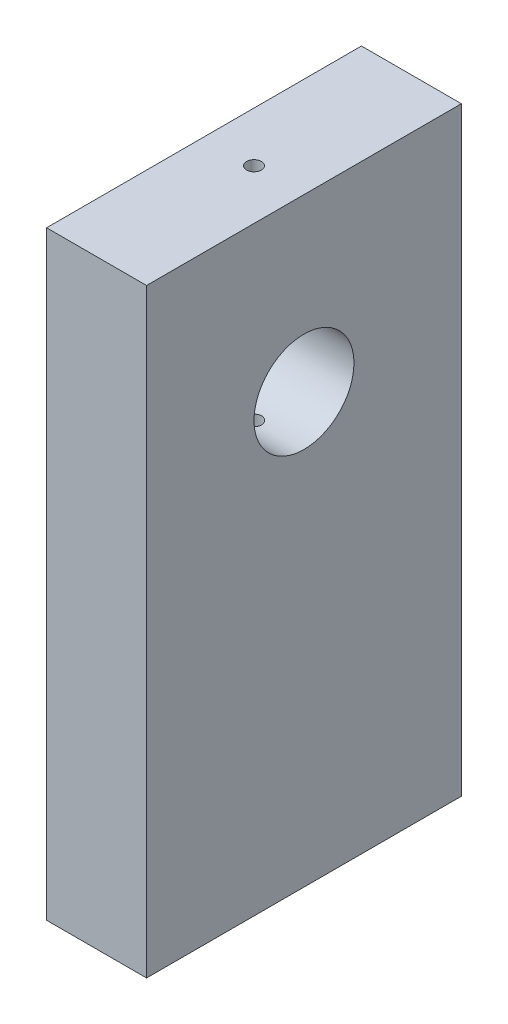
SolidWorks part; units mm, degrees
material "1060 Alloy"
ref_plane "Front Plane" through (0, 0, 0) normal (0, 0, 1) x (1, 0, 0)
ref_plane "Top Plane" through (0, 0, 0) normal (0, 1, 0) x (1, 0, 0)
ref_plane "Right Plane" through (0, 0, 0) normal (1, 0, 0) x (0, 0, -1)
sketch "Sketch11" plane through (0, 0, 0) normal (0, 1, 0) x (1, 0, 0)
  line L1 (0, -28.0311) -> (12.7, -28.0311)
  line L2 (0, -28.0311) -> (0, 11.9689)
  line L3 (0, 11.9689) -> (12.7, 11.9689)
  line L4 (12.7, -28.0311) -> (12.7, 11.9689)
  dimension "D1" = 12.7
extrude "Boss-Extrude2" add sketch "Sketch11" along normal blind 76.2
sketch "Sketch12" plane through (12.7, 0, 0) normal (1, 0, 0) x (0, 0, -1)
  line L1 (-8.0311, 76.2) -> (-8.0311, 1.8836) construction
  line L3 (-28.0311, 0) -> (11.9689, 0) construction
  line L5 (-28.0311, 76.2) -> (-28.0311, 0) construction
  circle A0 centre (-8.0311, 54.5) radius 6.35
  dimension "D2" = 12.7
  dimension "D1" = 20
  dimension "D3" = 54.5
extrude "Cut-Extrude5" cut sketch "Sketch12" against normal through all
sketch "Sketch13" plane through (0, 76.2, 0) normal (0, 1, 0) x (1, 0, 0)
  line L0 (0, -8.0311) -> (12.7, -8.0311) construction
  line L1 (0, 11.9689) -> (0, -28.0311) construction
  line L2 (12.7, -28.0311) -> (12.7, 11.9689) construction
  circle A0 centre (6.35, -8.0311) radius 0.95
  dimension "D1" = 1.9
extrude "Cut-Extrude6" cut sketch "Sketch13" against normal blind 30
sketch "Sketch17" plane through (0, 0, 0) normal (0, -1, 0) x (1, 0, 0)
  line L3 (12.7, -11.9689) -> (0, -11.9689) construction
  line L4 (0, -11.9689) -> (0, 28.0311) construction
  line L5 (0, 28.0311) -> (12.7, 28.0311) construction
  circle A0 centre (6.35, 14.6981) radius 0.95
  circle A1 centre (6.35, 1.3641) radius 0.95
  dimension "D1" = 1.9
  dimension "D2" = 1.9
  dimension "D7" = 13.333
  dimension "D8" = 6.35
  dimension "D9" = 6.35
  dimension "D10" = 13.333
extrude "Cut-Extrude8" cut sketch "Sketch17" against normal blind 21
